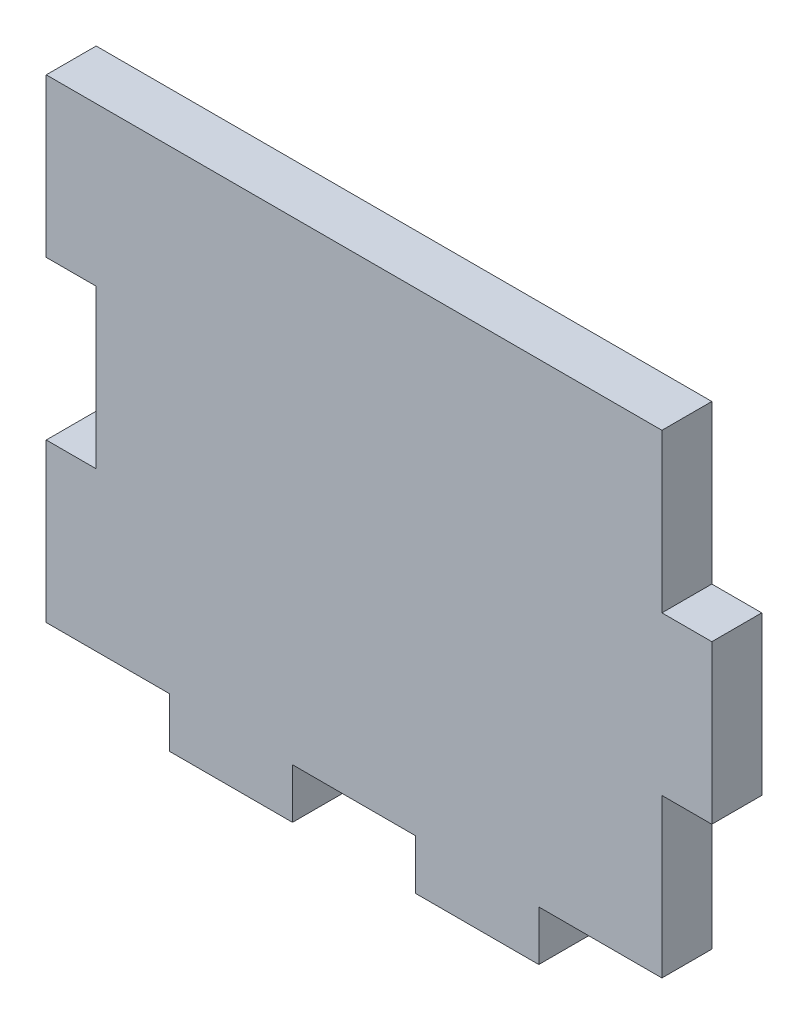
SolidWorks part; units mm, degrees
ref_plane "Front Plane" through (0, 0, 0) normal (0, 0, 1) x (1, 0, 0)
ref_plane "Top Plane" through (0, 0, 0) normal (0, 1, 0) x (1, 0, 0)
ref_plane "Right Plane" through (0, 0, 0) normal (1, 0, 0) x (0, 0, -1)
sketch "Sketch1" plane through (0, 0, 0) normal (0, 0, 1) x (1, 0, 0)
  line L0 (22.2, 0) -> (33.3, 0)
  line L1 (0, 0) -> (11.1, 0)
  line L2 (0, 0) -> (0, 14.2533)
  line L3 (0, 42.76) -> (20, 42.76)
  line L4 (55.5, 0) -> (55.5, 14.2533)
  line L5 (44.4, 0) -> (55.5, 0)
  line L6 (11.1, 0) -> (11.1, -4.5)
  line L7 (11.1, -4.5) -> (22.2, -4.5)
  line L8 (22.2, 0) -> (22.2, -4.5)
  line L9 (0, 28.5067) -> (0, 42.76)
  line L10 (33.3, 0) -> (33.3, -4.5)
  line L11 (33.3, -4.5) -> (44.4, -4.5)
  line L12 (44.4, 0) -> (44.4, -4.5)
  line L13 (55.5, 14.2533) -> (60, 14.2533)
  line L14 (40, 42.76) -> (55.5, 42.76)
  line L15 (55.5, 28.5067) -> (60, 28.5067)
  line L16 (60, 14.2533) -> (60, 28.5067)
  line L17 (0, 28.5067) -> (4.5, 28.5067)
  line L18 (55.5, 28.5067) -> (55.5, 42.76)
  line L19 (0, 14.2533) -> (4.5, 14.2533)
  line L20 (4.5, 28.5067) -> (4.5, 14.2533)
  line L21 (60, 42.76) -> (40, 42.76) construction
  line L22 (20, 42.76) -> (40, 42.76)
  line L25 (60, 39.1343) -> (60, 50039.1343) construction
  dimension "D1" = 4.5
  dimension "D2" = 60
  dimension "D3" = 42.76
extrude "Boss-Extrude1" add sketch "Sketch1" along normal blind 4.5
equation "\"D1@Sketch1\" = \"mat@v5.assembly\""
equation "\"D1@Boss-Extrude1\"=\"mat@v5.assembly\""
